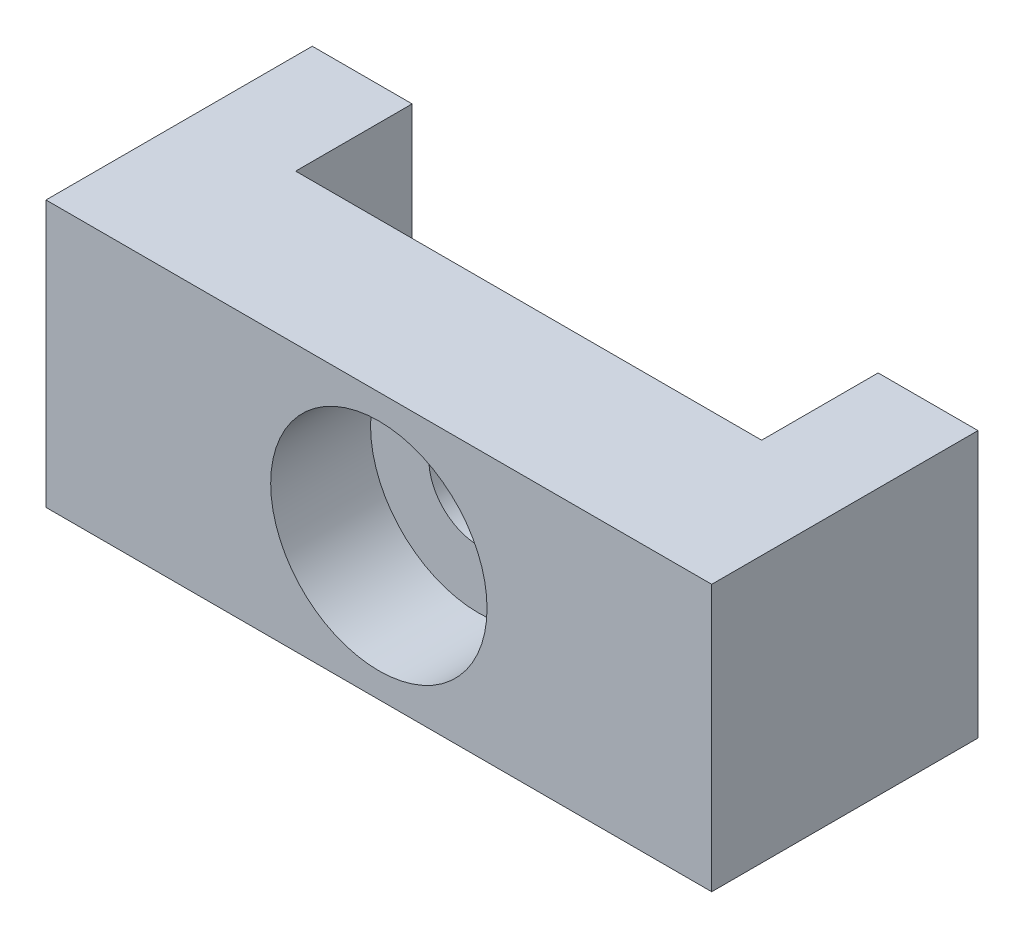
SolidWorks part; units mm, degrees
ref_plane "Front Plane" through (0, 0, 0) normal (0, 0, 1) x (1, 0, 0)
ref_plane "Top Plane" through (0, 0, 0) normal (0, 1, 0) x (1, 0, 0)
ref_plane "Right Plane" through (0, 0, 0) normal (1, 0, 0) x (0, 0, -1)
sketch "Sketch1" plane through (0, 0, 0) normal (0, 0, 1) x (1, 0, 0)
  line L1 (10, -4) -> (-10, -4)
  line L2 (10, -4) -> (10, 4)
  line L3 (10, 4) -> (-10, 4)
  line L4 (-10, -4) -> (-10, 4)
  line L5 (10, -4) -> (-10, 4) construction
  line L6 (10, 4) -> (-10, -4) construction
  point P0 (0, 0)
  dimension "D1" = 20
  dimension "D2" = 8
extrude "Extrude1" add sketch "Sketch1" against normal blind 8
sketch "Sketch2" plane through (0, 0, -8) normal (0, 0, -1) x (-1, 0, 0)
  line L0 (-10, 4) -> (10, 4) construction
  line L1 (-7, -4) -> (7, -4)
  line L2 (-7, -4) -> (-7, 4)
  line L3 (-7, 4) -> (7, 4)
  line L4 (7, -4) -> (7, 4)
  line L5 (-7, -4) -> (7, 4) construction
  line L6 (-7, 4) -> (7, -4) construction
  point P0 (0, 0)
  dimension "D1" = 14
extrude "Extrude2" cut sketch "Sketch2" against normal blind 3.5
sketch "Sketch5" plane through (0, 0, 0) normal (0, 0, 1) x (1, 0, 0)
  point P0 (0, 0)
hole_wizard "CBORE for M5 Hex Head Bolt1" positions "3DSketch2" profile "Sketch6" counterbore size "M5" standard "ISO" end condition through all
sketch3d "3DSketch2"
  point P0 (0, 0, 0)
  point P4 (0, 0, 0)
sketch "Sketch6" plane through (0, 0, 0) normal (1, 0, 0) x (0, -1, 0)
  line L0 (0, 0) -> (0, 8)
  line L1 (0, 8) -> (1.5, 8)
  line L3 (1.5, 8) -> (1.5, 3)
  line L4 (1.5, 3) -> (3.25, 3)
  line L5 (3.25, 3) -> (3.25, 0)
  line L7 (3.25, 0) -> (0, 0)
  line L11 (0, -6.35) -> (0, 107.95) construction
  dimension "Thru Hole Dia." = 3
  dimension "Thru Hole Depth" = 8
  dimension "C'Bore Dia." = 6.5
  dimension "C'Bore Depth" = 3
